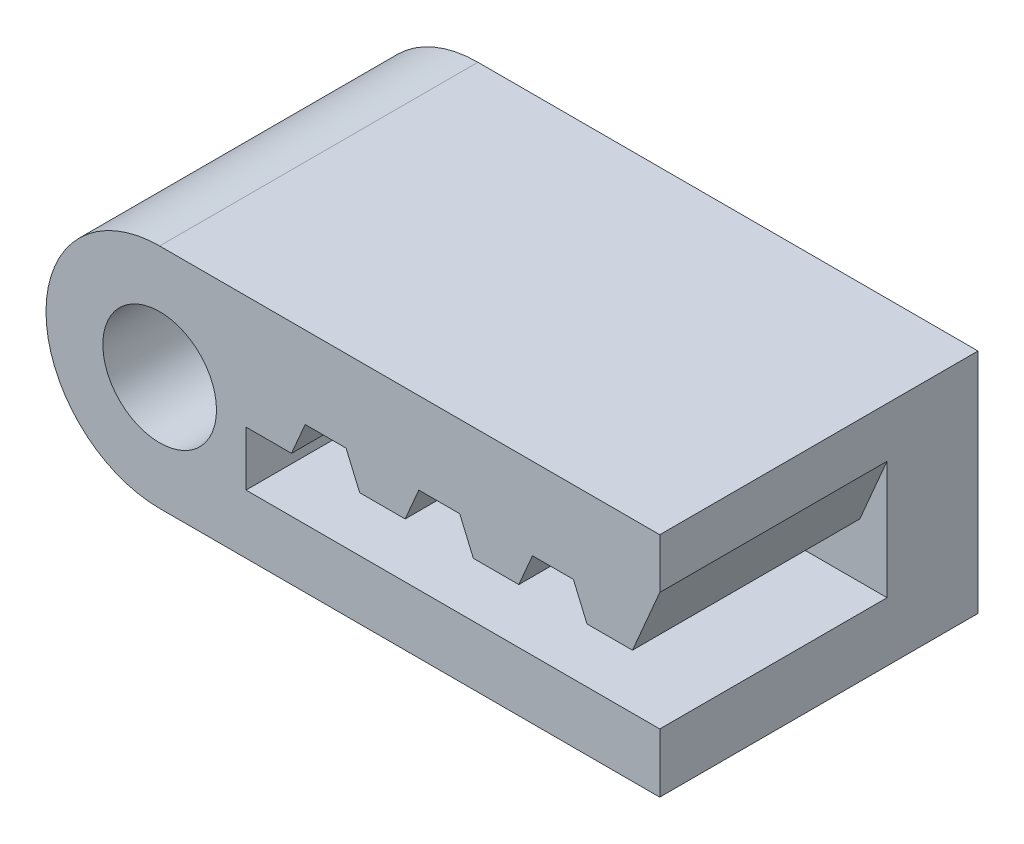
SolidWorks part; units mm, degrees
ref_plane "Front Plane" through (0, 0, 0) normal (0, 0, 1) x (1, 0, 0)
ref_plane "Top Plane" through (0, 0, 0) normal (0, 1, 0) x (1, 0, 0)
ref_plane "Right Plane" through (0, 0, 0) normal (1, 0, 0) x (0, 0, -1)
sketch "Sketch1" plane through (0, 0, 0) normal (0, 0, 1) x (1, 0, 0)
  line L1 (0, 0) -> (11, 0)
  line L3 (0, 5) -> (11, 5)
  line L4 (11, 0) -> (11, 5)
  arc A0 (0, 5) -> (0, 0) centre (0, 2.5) ccw
  dimension "D1" = 11
  dimension "D2" = 5
extrude "Boss-Extrude1" add sketch "Sketch1" along normal blind 7
sketch "Sketch2" plane through (0, 0, 7) normal (0, 0, 1) x (1, 0, 0)
  line L0 (0, 2.5) -> (11, 2.5) construction
  line L1 (0, 0) -> (0, 5) construction
  line L2 (11, 0) -> (11, 5) construction
  line L3 (11, 3.9) -> (10.4, 2.5)
  line L4 (10.4, 2.5) -> (9.4, 2.5)
  line L5 (9.4, 2.5) -> (9.1, 3.2)
  line L6 (9.1, 3.2) -> (8.2, 3.2)
  line L7 (8.2, 3.2) -> (7.9, 2.5)
  line L8 (7.9, 2.5) -> (6.9, 2.5)
  line L9 (6.9, 2.5) -> (6.6, 3.2)
  line L10 (6.6, 3.2) -> (5.7, 3.2)
  line L11 (5.7, 3.2) -> (5.4, 2.5)
  line L12 (5.4, 2.5) -> (4.4, 2.5)
  line L14 (1.9, 1.3) -> (11, 1.3)
  line L15 (11, 1.3) -> (11, 3.9)
  line L16 (4.4, 2.5) -> (4.1, 3.2)
  line L17 (4.1, 3.2) -> (3.2, 3.2)
  line L18 (3.2, 3.2) -> (2.9, 2.5)
  line L19 (2.9, 2.5) -> (1.9, 2.5)
  line L20 (1.9, 2.5) -> (1.9, 1.3)
  dimension "D1" = 1
  dimension "D2" = 0.3
  dimension "D3" = 0.9
  dimension "D4" = 0.6
  dimension "D5" = 0.7
  dimension "D6" = 1.9
extrude "Cut-Extrude1" cut sketch "Sketch2" against normal offset from surface (5 mm away) 2 up to face at (4.875, 2.5, 0)
sketch "Sketch3" plane through (0, 0, 7) normal (0, 0, 1) x (1, 0, 0)
  line L2 (0, 0) -> (0, 5) construction
  circle A0 centre (0, 2.5) radius 1.25
  dimension "D1" = 2.5
extrude "Cut-Extrude2" cut sketch "Sketch3" against normal through all
